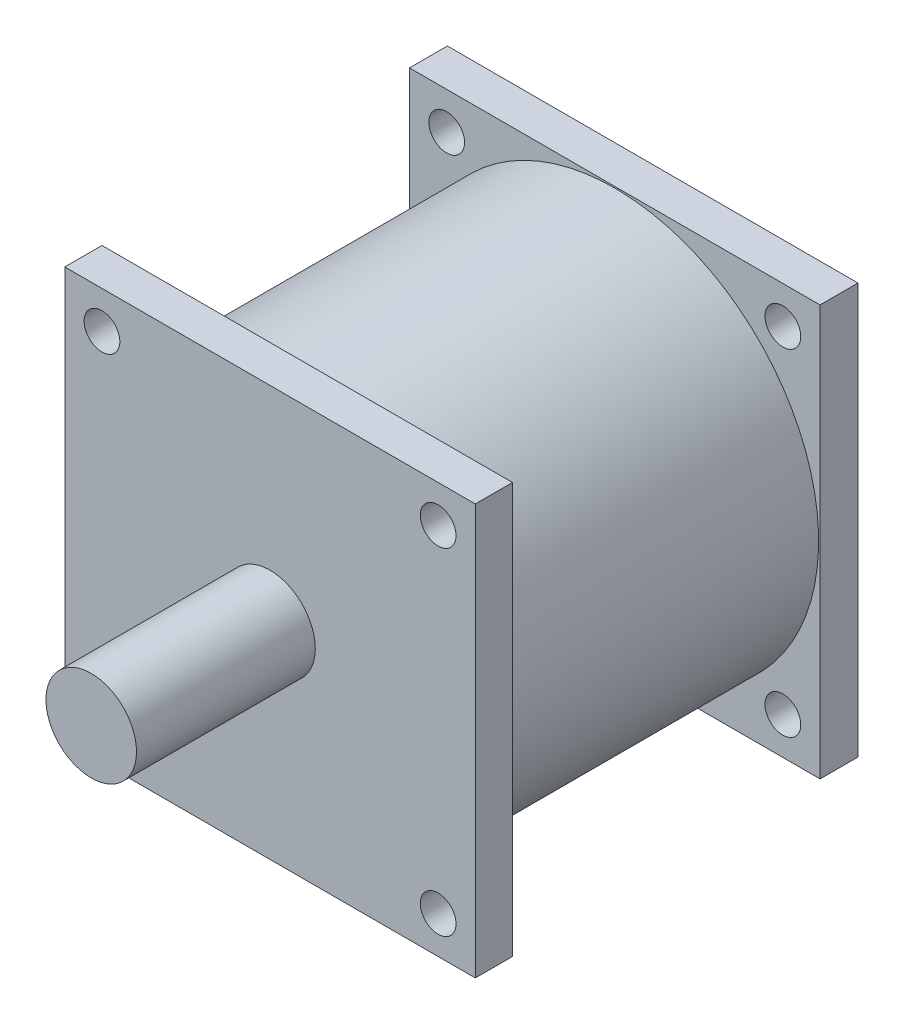
SolidWorks part; units mm, degrees
ref_plane "Ebene vorne" through (0, 0, 0) normal (0, 0, 1) x (1, 0, 0)
ref_plane "Ebene oben" through (0, 0, 0) normal (0, 1, 0) x (1, 0, 0)
ref_plane "Ebene rechts" through (0, 0, 0) normal (1, 0, 0) x (0, 0, -1)
sketch "Skizze1" plane through (0, 0, 0) normal (0, 0, 1) x (1, 0, 0)
  circle A0 centre (0, 0) radius 28.5
  dimension "D1" = 57
extrude "Aufsatz-Linear austragen1" add sketch "Skizze1" along normal blind 43
sketch "Skizze2" plane through (0, 0, 43) normal (0, 0, 1) x (1, 0, 0)
  line L0 (0, 0) -> (28.7, 0)
  line L1 (28.7, 0) -> (28.7, 28.7)
  line L2 (28.7, 28.7) -> (-28.7, 28.7)
  line L3 (-28.7, 28.7) -> (-28.7, -28.7)
  line L4 (-28.7, -28.7) -> (28.7, -28.7)
  line L5 (28.7, -28.7) -> (28.7, 0)
  dimension "D1" = 28.7
  dimension "D2" = 57.4
  dimension "D3" = 57.4
  dimension "D4" = 28.7
  dimension "D5" = 57.4
extrude "Aufsatz-Linear austragen2" add sketch "Skizze2" along normal blind 5.2 contours L1 L2 L3 L4 L5
sketch "Skizze3" plane through (0, 0, 0) normal (0, 0, -1) x (-1, 0, 0)
  line L0 (0, 0) -> (28.7, 0)
  line L1 (28.7, 0) -> (28.7, 28.7)
  line L2 (28.7, 28.7) -> (-28.7, 28.7)
  line L3 (-28.7, 28.7) -> (-28.7, -28.7)
  line L4 (-28.7, -28.7) -> (28.7, -28.7)
  line L5 (28.7, -28.7) -> (28.7, 0)
  dimension "D1" = 28.7
  dimension "D2" = 28.7
  dimension "D3" = 57.4
  dimension "D4" = 57.4
extrude "Aufsatz-Linear austragen3" add sketch "Skizze3" along normal blind 5.3 contours L1 L2 L3 L4 L5
sketch "Skizze4" plane through (0, 0, 48.2) normal (0, 0, 1) x (1, 0, 0)
  circle A0 centre (0, 0) radius 6.33
  dimension "D1" = 12.66
extrude "Aufsatz-Linear austragen4" add sketch "Skizze4" along normal blind 25
sketch "Skizze5" plane through (0, 0, 48.2) normal (0, 0, 1) x (1, 0, 0)
  line L0 (-28.7, -28.7) -> (28.7, -28.7) construction
  line L1 (-23.5, 23.5) -> (23.5, 23.5)
  line L2 (-23.5, 23.5) -> (-23.5, -23.5)
  line L3 (-23.5, -23.5) -> (23.5, -23.5)
  line L4 (23.5, 23.5) -> (23.5, -23.5)
  line L5 (-28.7, 28.7) -> (-28.7, -28.7) construction
  dimension "D1" = 47
  dimension "D2" = 47
  dimension "D3" = 5.2
  dimension "D4" = 5.2
hole_wizard "M6x1.0 Gewindebohrung1" positions "Skizze7" profile "Skizze8" tap size "M6x1.0" standard "ANSI Metrisch" end condition up to next
sketch "Skizze7" plane through (0, 0, 48.2) normal (0, 0, 1) x (1, 0, 0)
  point P0 (-23.5, 23.5)
  point P3 (23.5, 23.5)
  point P6 (23.5, -23.5)
  point P9 (-23.5, -23.5)
sketch "Skizze8" plane through (-23.5, 23.5, 48.2) normal (1, 0, 0) x (0, -1, 0)
  line L0 (0, 0) -> (0, 5.2)
  line L1 (0, 5.2) -> (2.5, 5.2)
  line L2 (2.5, 5.2) -> (2.5, 0)
  line L5 (2.5, 0) -> (0, 0)
  line L11 (0, -6.35) -> (0, 107.95) construction
  dimension "Bohrerdurchmesser" = 5
  dimension "Bohrungstiefe" = 5.2
cosmetic thread "Bohrungsgewinde1" parameters "D2"=6
cosmetic thread "Bohrungsgewinde2" parameters "D2"=6
cosmetic thread "Bohrungsgewinde3" parameters "D2"=6
cosmetic thread "Bohrungsgewinde4" parameters "D2"=6
hole_wizard "Ø5.0 (5) Durchmesser Bohrung1" positions "Skizze10" profile "Skizze11" hole size "Ø5.0" standard "ANSI Metrisch" end condition through all
sketch "Skizze10" plane through (0, 0, 48.2) normal (0, 0, 1) x (1, 0, 0)
  point P0 (-23.5, 23.5)
  point P3 (23.5, 23.5)
  point P6 (23.5, -23.5)
  point P9 (-23.5, -23.5)
sketch "Skizze11" plane through (-23.5, 23.5, 48.2) normal (1, 0, 0) x (0, -1, 0)
  line L0 (0, 0) -> (0, 53.5)
  line L1 (0, 53.5) -> (2.5, 53.5)
  line L2 (2.5, 53.5) -> (2.5, 0)
  line L5 (2.5, 0) -> (0, 0)
  line L11 (0, -6.35) -> (0, 107.95) construction
  dimension "Bohrerdurchmesser" = 5
  dimension "Bohrungstiefe" = 53.5
